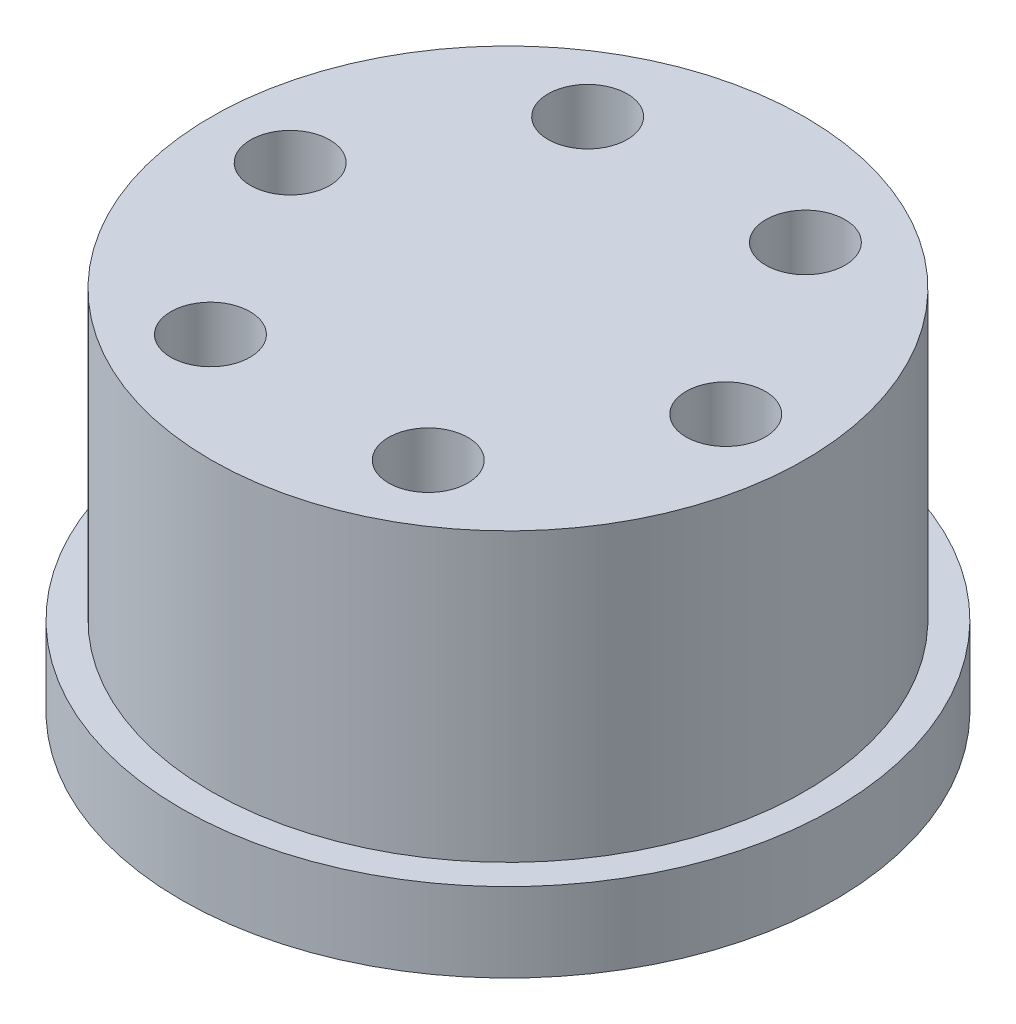
SolidWorks part; units mm, degrees
ref_plane "Front Plane" through (0, 0, 0) normal (0, 0, 1) x (1, 0, 0)
ref_plane "Top Plane" through (0, 0, 0) normal (0, 1, 0) x (1, 0, 0)
ref_plane "Right Plane" through (0, 0, 0) normal (1, 0, 0) x (0, 0, -1)
sketch "Sketch1" plane through (0, 0, 0) normal (0, 1, 0) x (1, 0, 0)
  circle A0 centre (0, 0) radius 16.5
  circle A1 centre (0, 0) radius 12.5 construction
  circle A2 centre (0, 12.5) radius 1.65
  circle A3 centre (10.8253, 6.25) radius 1.65
  circle A4 centre (10.8253, -6.25) radius 1.65
  circle A5 centre (0, -12.5) radius 1.65
  circle A6 centre (-10.8253, -6.25) radius 1.65
  circle A7 centre (-10.8253, 6.25) radius 1.65
  point P19 (0, 0)
  dimension "D1" = 33
  dimension "D2" = 25
  dimension "D3" = 3.3
  dimension "D4" = 6
extrude "Boss-Extrude1" add sketch "Sketch1" along normal blind 4
sketch "Sketch2" plane through (0, 4, 0) normal (0, 1, 0) x (1, 0, 0)
  circle A0 centre (0, 0) radius 15
  dimension "D1" = 30
extrude "Boss-Extrude2" add sketch "Sketch2" along normal blind 14.5
sketch "Sketch5" plane through (0, 18.5, 0) normal (0, 1, 0) x (1, 0, 0)
  circle A0 centre (0, 0) radius 11 construction
  circle A1 centre (-11, 0) radius 2
  circle A2 centre (-5.5, 9.5263) radius 2
  circle A3 centre (5.5, 9.5263) radius 2
  circle A4 centre (11, 0) radius 2
  circle A5 centre (5.5, -9.5263) radius 2
  circle A6 centre (-5.5, -9.5263) radius 2
  point P17 (0, 0)
  dimension "D1" = 22
  dimension "D2" = 4
  dimension "D3" = 6
extrude "Cut-Extrude3" cut sketch "Sketch5" against normal blind 6.5
sketch "Sketch6" plane through (0, 0, 0) normal (0, -1, 0) x (1, 0, 0)
  circle A0 centre (0, 0) radius 7.6
  dimension "D1" = 15.2
extrude "Cut-Extrude4" cut sketch "Sketch6" against normal blind 5
